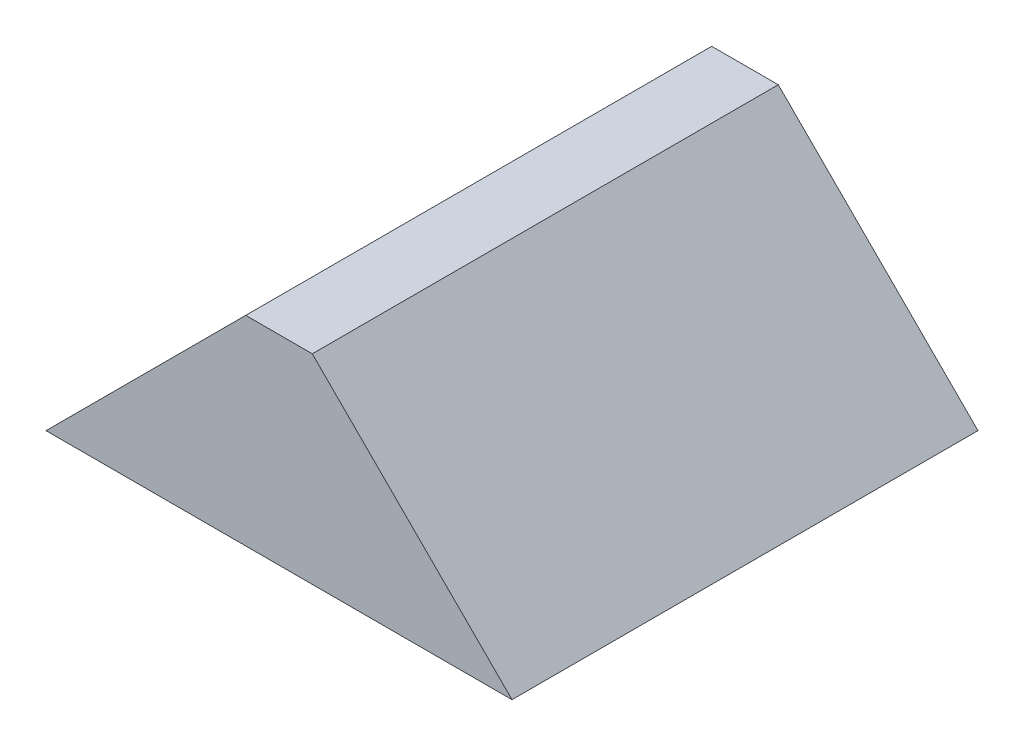
SolidWorks part; units mm, degrees
material "Pine"
ref_plane "Front Plane" through (0, 0, 0) normal (0, 0, 1) x (1, 0, 0)
ref_plane "Top Plane" through (0, 0, 0) normal (0, 1, 0) x (1, 0, 0)
ref_plane "Right Plane" through (0, 0, 0) normal (1, 0, 0) x (0, 0, -1)
sketch "Sketch1" plane through (0, 0, 0) normal (0, 1, 0) x (1, 0, 0)
  line L1 (0, 0) -> (88.9, 0)
  line L2 (0, 0) -> (0, 88.9)
  line L3 (0, 88.9) -> (88.9, 88.9)
  line L4 (88.9, 0) -> (88.9, 88.9)
  dimension "D1" = 88.9
  dimension "D2" = 88.9
extrude "Boss-Extrude1" add sketch "Sketch1" along normal blind 38.1
sketch "Sketch2" plane through (0, 0, 0) normal (0, 0, 1) x (1, 0, 0)
  line L0 (0, 0) -> (38.1, 38.1)
  line L1 (0, 38.1) -> (88.9, 38.1) construction
  line L2 (38.1, 38.1) -> (0, 38.1)
  line L3 (0, 38.1) -> (0, 0)
  line L5 (88.9, 0) -> (88.9, 38.1)
  line L9 (88.9, 38.1) -> (50.8, 38.1)
  line L10 (50.8, 38.1) -> (88.9, 0)
  dimension "D1" = 38.1
  dimension "D2" = 38.1
  dimension "D3" = 38.1
extrude "Cut-Extrude1" cut sketch "Sketch2" against normal through all
